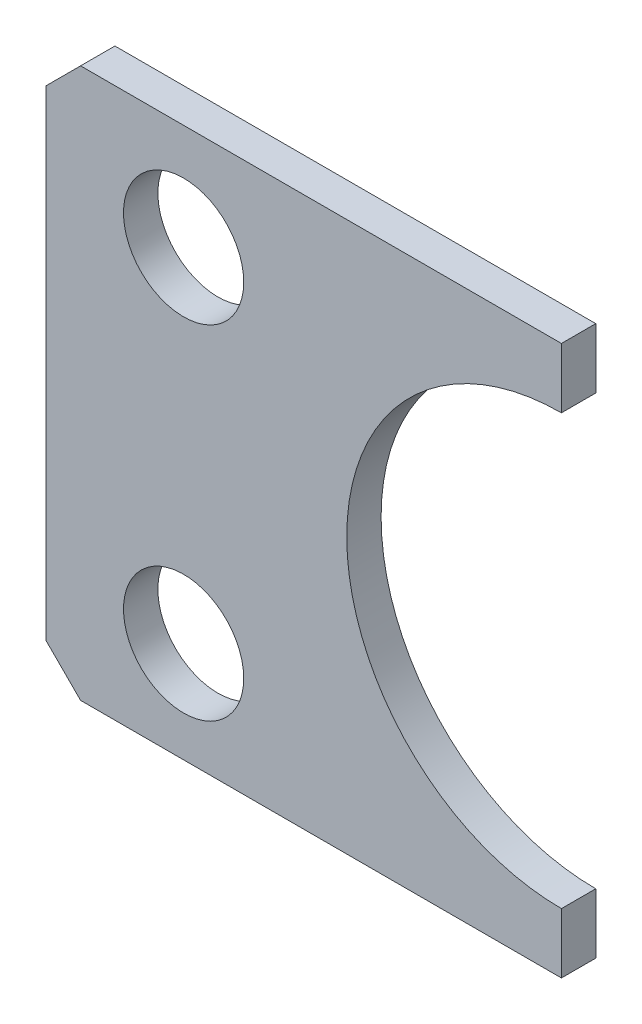
SolidWorks part; units mm, degrees
ref_plane "Front Plane" through (0, 0, 0) normal (0, 0, 1) x (1, 0, 0)
ref_plane "Top Plane" through (0, 0, 0) normal (0, 1, 0) x (1, 0, 0)
ref_plane "Right Plane" through (0, 0, 0) normal (1, 0, 0) x (0, 0, -1)
sketch "Sketch1" plane through (0, 0, 0) normal (0, 0, 1) x (1, 0, 0)
  line L0 (7.5, -6.25) -> (7.5, -8)
  line L1 (-7.5, 8) -> (7.5, 8)
  line L2 (-7.5, 8) -> (-7.5, -8)
  line L3 (-7.5, -8) -> (7.5, -8)
  line L4 (7.5, 8) -> (7.5, 6.25)
  line L5 (-7.5, 8) -> (7.5, -8) construction
  line L6 (-7.5, -8) -> (7.5, 8) construction
  arc A0 (7.5, 6.25) -> (7.5, -6.25) centre (7.5, 0) ccw
  circle A1 centre (-3.5, 4.9201) radius 1.75
  circle A2 centre (-3.5, -5.07) radius 1.75
  point P0 (0, 0)
  point P12 (0, 0)
  dimension "D1" = 6.25
  dimension "D4" = 3.5
  dimension "D2" = 16
  dimension "D3" = 15
  dimension "D5" = 4
extrude "Boss-Extrude1" add sketch "Sketch1" along normal blind 1
chamfer "Chamfer1" distance 1 angle 45 2 edges at (-7.5, -8, 0.5) (-7.5, 8, 0.5)
